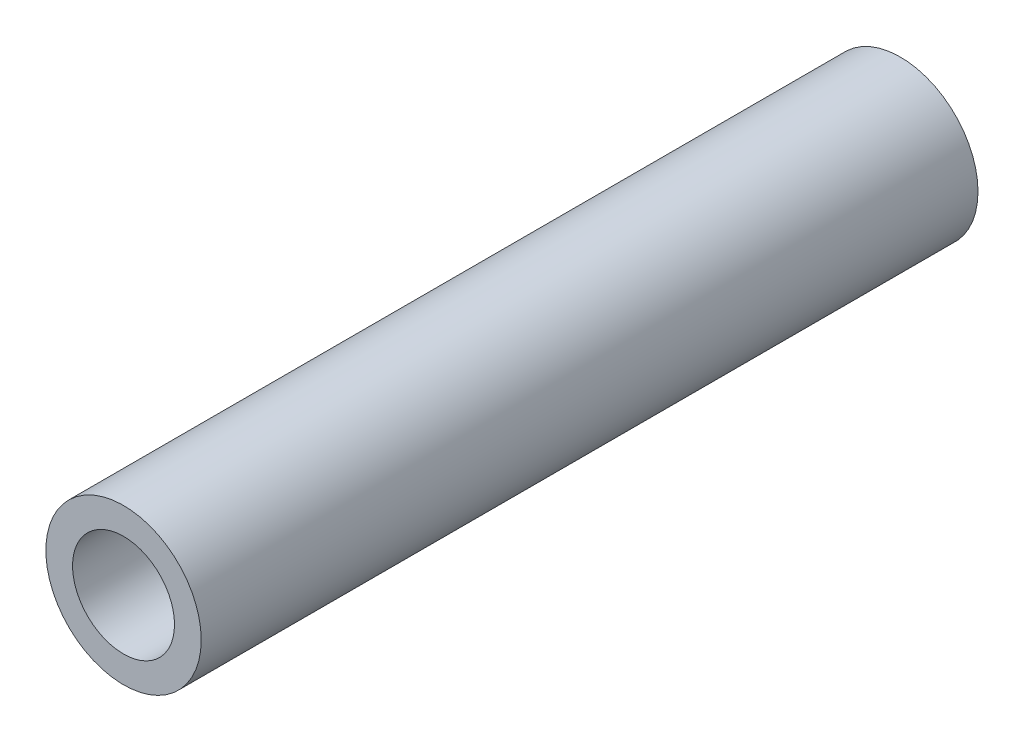
SolidWorks part; units mm, degrees
material "Plain Carbon Steel"
ref_plane "Front Plane" through (0, 0, 0) normal (0, 0, 1) x (1, 0, 0)
ref_plane "Top Plane" through (0, 0, 0) normal (0, 1, 0) x (1, 0, 0)
ref_plane "Right Plane" through (0, 0, 0) normal (1, 0, 0) x (0, 0, -1)
sketch "Sketch1" plane through (0, 0, 0) normal (0, 0, 1) x (1, 0, 0)
  circle A0 centre (0, 0) radius 12.7
  circle A1 centre (0, 0) radius 8.3337
  dimension "D1" = 25.4
  dimension "D2" = 16.6675
extrude "Boss-Extrude1" add sketch "Sketch1" along normal blind 127
